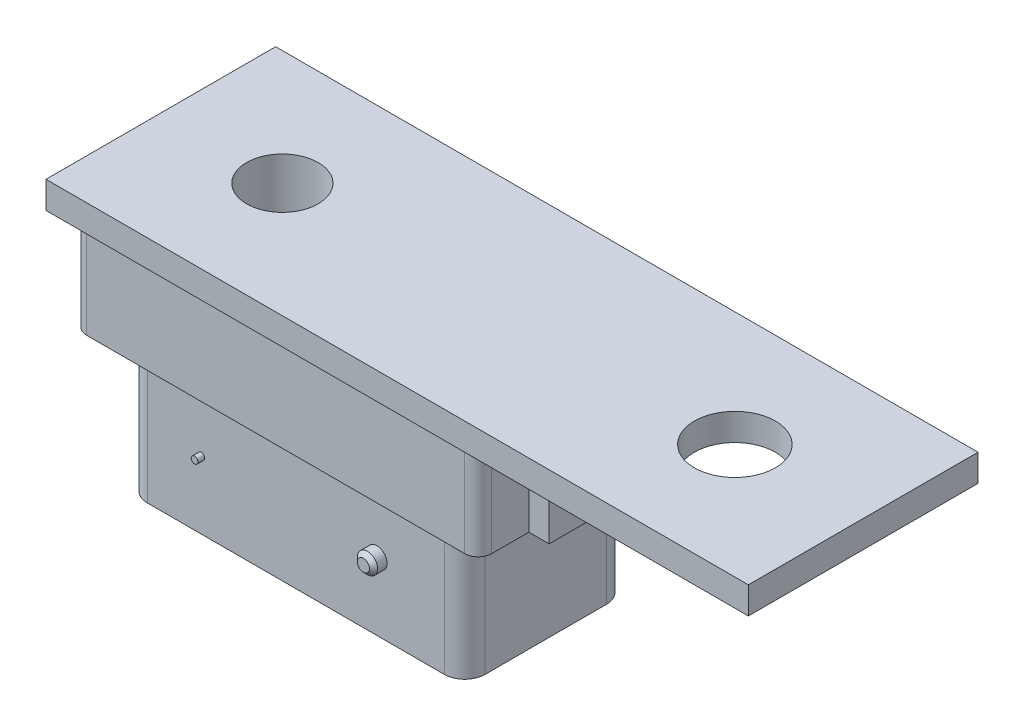
SolidWorks part; units mm, degrees
ref_plane "Front Plane" through (0, 0, 0) normal (0, 0, 1) x (1, 0, 0)
ref_plane "Top Plane" through (0, 0, 0) normal (0, 1, 0) x (1, 0, 0)
ref_plane "Right Plane" through (0, 0, 0) normal (1, 0, 0) x (0, 0, -1)
sketch "Sketch1" plane through (0, 0, 0) normal (0, 1, 0) x (1, 0, 0)
  line L1 (-260, -85) -> (260, -85)
  line L2 (-260, -85) -> (-260, 85)
  line L3 (-260, 85) -> (260, 85)
  line L4 (260, -85) -> (260, 85)
  line L5 (-260, -85) -> (260, 85) construction
  line L6 (-260, 85) -> (260, -85) construction
  point P0 (0, 0)
  dimension "D1" = 520
  dimension "D2" = 170
extrude "Boss-Extrude1" add sketch "Sketch1" along normal mid plane 20
sketch "Sketch2" plane through (0, -10, 0) normal (0, -1, 0) x (1, 0, 0)
  line L0 (-260, 85) -> (260, 85) construction
  line L1 (-240, 75) -> (40, 75)
  line L2 (-250, 65) -> (-250, -65)
  line L3 (-240, -75) -> (40, -75)
  line L4 (50, 65) -> (50, -65)
  line L5 (-260, -85) -> (-260, 85) construction
  arc A0 (-250, -65) -> (-240, -75) centre (-240, -65) ccw
  arc A1 (40, -75) -> (50, -65) centre (40, -65) ccw
  arc A2 (50, 65) -> (40, 75) centre (40, 65) ccw
  arc A3 (-240, 75) -> (-250, 65) centre (-240, 65) ccw
  point P10 (-250, -75)
  point P15 (50, 75)
  point P18 (-250, 75)
  dimension "D5" = 10
  dimension "D1" = 300
  dimension "D2" = 150
  dimension "D3" = 10
  dimension "D4" = 10
extrude "Boss-Extrude2" add sketch "Sketch2" along normal blind 75
sketch "Sketch3" plane through (0, -85, 0) normal (0, -1, 0) x (1, 0, 0)
  line L0 (0, 0) -> (-366.1, 0) construction
  line L1 (-210, 60) -> (10, 60)
  line L2 (-225, 45) -> (-225, -45)
  line L3 (-210, -60) -> (10, -60)
  line L4 (25, 45) -> (25, -45)
  line L5 (50, -65) -> (50, 65) construction
  arc A0 (25, -45) -> (10, -60) centre (10, -45) cw
  arc A1 (-210, -60) -> (-225, -45) centre (-210, -45) cw
  arc A2 (25, 45) -> (10, 60) centre (10, 45) ccw
  arc A3 (-210, 60) -> (-225, 45) centre (-210, 45) ccw
  point P13 (-225, -60)
  point P16 (25, 60)
  point P19 (-225, 60)
  dimension "D4" = 15
  dimension "D1" = 250
  dimension "D2" = 120
  dimension "D3" = 25
extrude "Boss-Extrude3" add sketch "Sketch3" along normal blind 100
sketch "Sketch4" plane through (-225, 0, 0) normal (-1, 0, 0) x (0, 0, 1)
  line L0 (0, -185) -> (0, -85) construction
  line L1 (45, -185) -> (-45, -185) construction
  line L2 (45, -85) -> (-45, -85) construction
  line L3 (10, -115) -> (10, -155)
  line L4 (-17.5015, -115) -> (-10, -115)
  line L5 (-17.5015, -115) -> (-17.5015, -155)
  line L6 (-17.5015, -155) -> (-10, -155)
  line L7 (-10, -115) -> (-10, -155)
  line L8 (17.5015, -155) -> (10, -155)
  line L9 (17.5015, -115) -> (17.5015, -155)
  line L10 (17.5015, -115) -> (10, -115)
  dimension "D1" = 7.5015
  dimension "D2" = 40
  dimension "D3" = 10
  dimension "D4" = 30
extrude "Boss-Extrude4" add sketch "Sketch4" along normal blind 25
sketch "Sketch5" plane through (0, 0, -17.5015) normal (0, 0, -1) x (-1, 0, 0)
  line L0 (250, -115) -> (250, -155) construction
  line L2 (250, -155) -> (225, -155) construction
  circle A0 centre (235, -135) radius 3.75
  dimension "D1" = 7.5
  dimension "D2" = 15
  dimension "D3" = 20
extrude "Cut-Extrude1" cut sketch "Sketch5" against normal blind 93
sketch "Sketch6" plane through (-250, 0, 0) normal (-1, 0, 0) x (0, 0, 1)
  line L0 (0, -85) -> (0, 0) construction
  line L1 (45, -85) -> (-45, -85) construction
  line L2 (-85, -10) -> (85, -10) construction
  line L3 (-25, -10) -> (25, -10)
  line L4 (-25, -10) -> (-25, -85)
  line L5 (-25, -85) -> (25, -85)
  line L6 (25, -10) -> (25, -85)
  line L7 (65, -85) -> (-65, -85) construction
  dimension "D1" = 50
extrude "Boss-Extrude5" add sketch "Sketch6" along normal blind 5
sketch "Sketch7" plane through (0, -10, 0) normal (0, -1, 0) x (1, 0, 0)
  line L0 (260, 85) -> (260, -85) construction
  circle A0 centre (165, 0) radius 30
  dimension "D1" = 60
  dimension "D2" = 95
extrude "Cut-Extrude2" cut sketch "Sketch7" against normal blind 68
sketch "Sketch8" plane through (50, 0, 0) normal (1, 0, 0) x (0, 0, -1)
  line L0 (0, 0) -> (0, -137.8388) construction
  line L1 (65, -10) -> (-65, -10) construction
  line L2 (-37.5, -10) -> (37.5, -10)
  line L3 (-37.5, -10) -> (-37.5, -85)
  line L4 (-37.5, -85) -> (37.5, -85)
  line L5 (37.5, -10) -> (37.5, -85)
  line L6 (65, -85) -> (-65, -85) construction
  dimension "D1" = 75
extrude "Boss-Extrude6" add sketch "Sketch8" along normal blind 15
sketch "Sketch9" plane through (0, -185, 0) normal (0, -1, 0) x (1, 0, 0)
  line L0 (25, -45) -> (25, 45) construction
  circle A0 centre (-35, 0) radius 30
  circle A1 centre (-35, 0) radius 26.5
  dimension "D1" = 60
  dimension "D3" = 53
  dimension "D2" = 60
extrude "Boss-Extrude7" add sketch "Sketch9" along normal blind 5
sketch "Sketch11" plane through (0, -185, 0) normal (0, -1, 0) x (1, 0, 0)
  circle A0 centre (-35, 0) radius 26.5 construction
  circle A1 centre (-35, 0) radius 26.5
extrude "Cut-Extrude3" cut sketch "Sketch11" against normal blind 75
sketch "Sketch12" plane through (0, -185, 0) normal (0, -1, 0) x (1, 0, 0)
  line L0 (-225, 45) -> (-225, -45) construction
  circle A0 centre (-170, 0) radius 26.5
  dimension "D1" = 53
  dimension "D2" = 55
extrude "Cut-Extrude4" cut sketch "Sketch12" against normal through all contours A0
sketch "Sketch13" plane through (0, 10, 0) normal (0, 1, 0) x (1, 0, 0)
  line L0 (-170, 0) -> (165, 0) construction
sketch "Sketch14" plane through (0, 0, 60) normal (0, 0, 1) x (1, 0, 0)
  line L0 (10, -185) -> (-210, -185) construction
  line L1 (10, -185) -> (10, -85) construction
  circle A0 centre (-40, -135) radius 7.5
  dimension "D1" = 15
  dimension "D3" = 50
  dimension "D2" = 50
extrude "Boss-Extrude8" add sketch "Sketch14" along normal blind 10
chamfer "Chamfer1" distance 3 angle 45 1 edges at (-32.5, -135, 70)
sketch "Sketch15" plane through (0, 0, 60) normal (0, 0, 1) x (1, 0, 0)
  line L0 (10, -185) -> (-210, -185) construction
  circle A0 centre (-170, -135) radius 2.5
  circle A1 centre (-40, -135) radius 4.5 construction
  dimension "D1" = 5
  dimension "D2" = 130
  dimension "D3" = 50
extrude "Boss-Extrude9" add sketch "Sketch15" along normal blind 5
ref_plane "Plane1" through (0, 0, 100) normal (0, 0, 1) x (1, 0, 0)
